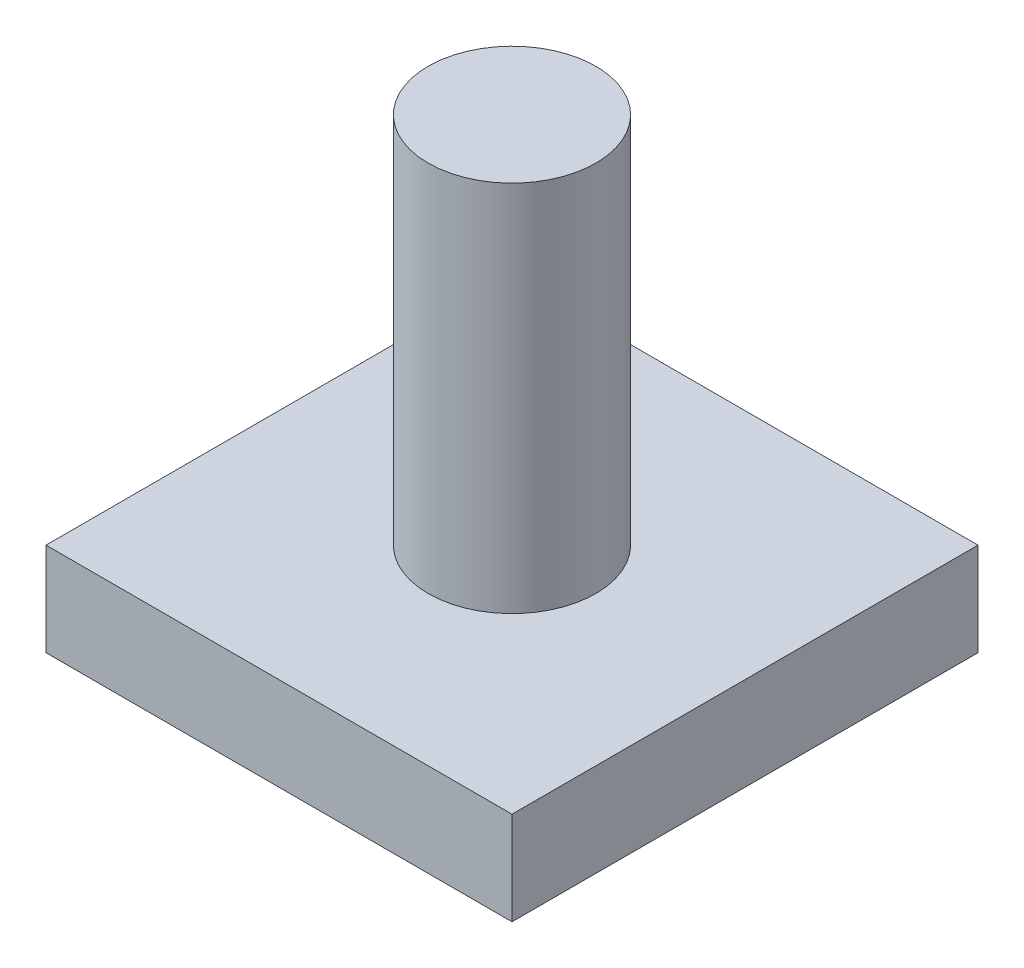
SolidWorks part; units mm, degrees
ref_plane "Front Plane" through (0, 0, 0) normal (0, 0, 1) x (1, 0, 0)
ref_plane "Top Plane" through (0, 0, 0) normal (0, 1, 0) x (1, 0, 0)
ref_plane "Right Plane" through (0, 0, 0) normal (1, 0, 0) x (0, 0, -1)
sketch "Sketch1" plane through (0, 0, 0) normal (0, 1, 0) x (1, 0, 0)
  line L1 (-2.5, 2.5) -> (2.5, 2.5)
  line L2 (-2.5, 2.5) -> (-2.5, -2.5)
  line L3 (-2.5, -2.5) -> (2.5, -2.5)
  line L4 (2.5, 2.5) -> (2.5, -2.5)
  line L5 (-2.5, 2.5) -> (2.5, -2.5) construction
  line L6 (-2.5, -2.5) -> (2.5, 2.5) construction
  point P0 (0, 0)
extrude "Boss-Extrude1" add sketch "Sketch1" along normal blind 1
sketch "Sketch2" plane through (0, 0, 0) normal (0, 1, 0) x (1, 0, 0)
  circle A0 centre (0, 0) radius 0.9
extrude "Boss-Extrude2" add sketch "Sketch2" along normal blind 5 contours A0
